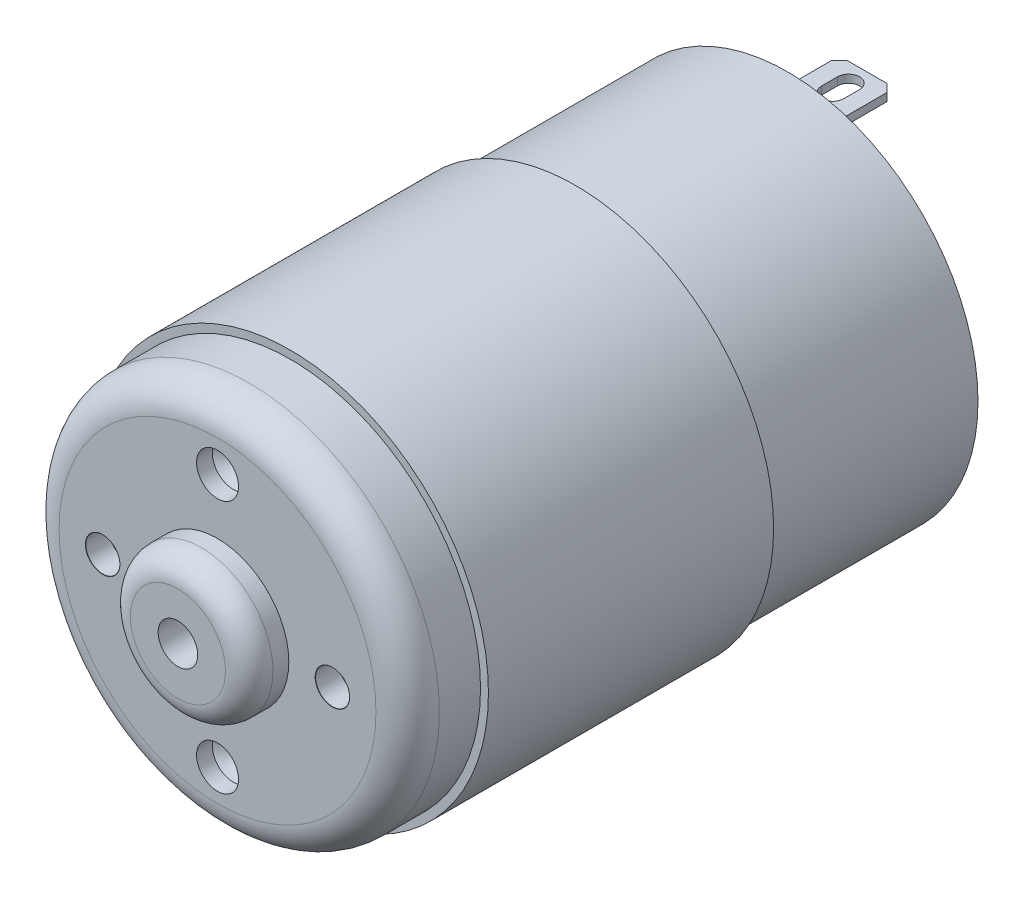
SolidWorks part; units mm, degrees
ref_plane "Front Plane" through (0, 0, 0) normal (1, 0, 0) x (0, 1, 0)
ref_plane "Top Plane" through (0, 0, 0) normal (0, 0, 1) x (0, 1, 0)
ref_plane "Right Plane" through (0, 0, 0) normal (0, 1, 0) x (-1, 0, 0)
sketch "Sketch1" plane through (0, 0, 0) normal (0, 0, 1) x (0, 1, 0)
  circle A0 centre (0, 0) radius 24
  dimension "D1" = 48
extrude "Boss-Extrude1" add sketch "Sketch1" along normal blind 72 contours A0
ref_plane "Plane1" through (0, 0, 72) normal (0, 0, 1) x (1, 0, 0)
sketch "Sketch6" plane through (0, 0, 72) normal (0, 0, 1) x (1, 0, 0)
  circle A0 centre (0, 0) radius 9
  dimension "D1" = 18
extrude "Boss-Extrude2" add sketch "Sketch6" along normal blind 5
sketch "Sketch7" plane through (0, 0, 0) normal (0, 0, 1) x (0, 1, 0)
  circle A0 centre (0, 0) radius 9
extrude "Boss-Extrude3" add sketch "Sketch7" against normal blind 5
ref_plane "Plane2" through (0, 0, 77) normal (0, 0, 1) x (1, 0, 0)
sketch "Sketch8" plane through (0, 0, 77) normal (0, 0, 1) x (1, 0, 0)
  circle A0 centre (0, 0) radius 2.5
  dimension "D1" = 5
extrude "Cut-Extrude5" cut sketch "Sketch8" against normal up to surface (82 mm away) up to face at (9, 0, -5)
fillet "Fillet3" radius 3 2 edges at (9, 0, -5) (9, 0, 77)
fillet "Fillet4" radius 4 1 edges at (24, 0, 72)
sketch "Sketch9" plane through (0, 0, 72) normal (0, 0, 1) x (1, 0, 0)
  circle A0 centre (0, 0) radius 24
  circle A1 centre (0, 0) radius 25
  dimension "D1" = 50
extrude "Boss-Extrude4" add sketch "Sketch9" against normal blind 36 from offset 9.2 offset against normal yes
sketch "Sketch10" plane through (0, 0, 0) normal (0, 0, 1) x (0, 1, 0)
  line L1 (-18, 3.5) -> (-19, 3.5)
  line L2 (-18, 3.5) -> (-18, -3.5)
  line L3 (-18, -3.5) -> (-19, -3.5)
  line L4 (-19, 3.5) -> (-19, -3.5)
  line L5 (18, -3.5) -> (19, -3.5)
  line L6 (19, 3.5) -> (19, -3.5)
  line L7 (18, 3.5) -> (19, 3.5)
  line L8 (18, 3.5) -> (18, -3.5)
  point P4 (-18, 0)
  dimension "D1" = 18
  dimension "D2" = 0
  dimension "D3" = 7
  dimension "D4" = 1
extrude "Boss-Extrude5" add sketch "Sketch10" against normal blind 10
sketch "Sketch15" plane through (0, 0, 72) normal (0, 0, 1) x (1, 0, 0)
  point P0 (0, 0)
  point P5 (-14.5, 0)
  point P7 (14.5, 0)
  dimension "D1" = 14.5
  dimension "D2" = 14.5
hole_wizard "M4 Clearance Hole5" positions "Sketch15" profile "Sketch18" hole size "M4" standard "ISO"
sketch "Sketch18" plane through (14.5, 0, 72) normal (1, 0, 0) x (0, -1, 0)
  line L0 (0, 0) -> (0, 4.2919)
  line L1 (0, 4.2919) -> (2.15, 3)
  line L2 (2.15, 3) -> (2.15, 0.025)
  line L3 (2.15, 0.025) -> (2.175, 0)
  line L5 (2.175, 0) -> (0, 0)
  line L6 (-2.15, 0.025) -> (-2.175, 0) construction
  line L10 (0, 4.2919) -> (-2.15, 3) construction
  line L11 (0, -6.35) -> (0, 107.95) construction
  dimension "Hole Dia." = 4.3
  dimension "Hole Depth" = 3
  dimension "Near C'Sink Dia." = 4.35
  dimension "Near C'Sink Angle" = 90
  dimension "Drill Angle" = 118
sketch "Sketch19" plane through (0, 0, 77) normal (0, 0, 1) x (1, 0, 0)
  point P0 (0, 16)
  point P5 (0, 0)
  point P7 (0, -16)
  dimension "D1" = 16
  dimension "D2" = 16
hole_wizard "M5 Clearance Hole1" positions "Sketch19" profile "Sketch20" hole size "M5" standard "ISO"
sketch "Sketch20" plane through (0, 16, 77) normal (1, 0, 0) x (0, -1, 0)
  line L0 (0, 0) -> (0, 8.5923)
  line L1 (0, 8.5923) -> (2.65, 7)
  line L2 (2.65, 7) -> (2.65, 0.025)
  line L3 (2.65, 0.025) -> (2.675, 0)
  line L5 (2.675, 0) -> (0, 0)
  line L6 (-2.65, 0.025) -> (-2.675, 0) construction
  line L10 (0, 8.5923) -> (-2.65, 7) construction
  line L11 (0, -6.35) -> (0, 107.95) construction
  dimension "Hole Dia." = 5.3
  dimension "Hole Depth" = 7
  dimension "Near C'Sink Dia." = 5.35
  dimension "Near C'Sink Angle" = 90
  dimension "Drill Angle" = 118
sketch "Sketch21" plane through (0, -19, 0) normal (0, -1, 0) x (1, 0, 0)
  line L0 (-3, -0.0166) -> (-3, -1.8436)
  line L1 (-3, -1.8436) -> (-3.5, -2.3)
  line L2 (-3.5, -2.3) -> (-3.5, -9)
  line L3 (-3.5, -9) -> (-2.5873, -10)
  line L4 (-2.5873, -10) -> (2.5, -10)
  line L5 (2.5, -10) -> (3.5, -9)
  line L6 (3.5, -9) -> (3.5, -2.3)
  line L7 (3.5, -2.3) -> (3, -1.8)
  line L8 (3, -1.8) -> (3, -0.0166)
  line L9 (3, -0.0166) -> (-3, -0.0166)
  line L10 (-3.5, -10) -> (-3.5, 0) construction
  line L12 (-3.5, -10) -> (3.5, -10) construction
  line L13 (-3.5, -2.3) -> (-3.5, 0)
  line L14 (-3.5, 0) -> (-3, -0.0166)
  line L15 (3, -0.0166) -> (3.5, 0)
  line L16 (3.5, 0) -> (3.5, -2.3)
  line L17 (3.5, -9) -> (3.5, -10)
  line L18 (3.5, -10) -> (2.5, -10)
  line L19 (-3.5, -9) -> (-3.5, -10)
  line L20 (-3.5, -10) -> (-2.5873, -10)
  line L21 (0, -7.5) -> (0, -5.5) construction
  line L22 (-1.3944, -7.5) -> (-1.3944, -5.5)
  line L23 (1.3944, -7.5) -> (1.3944, -5.5)
  arc A0 (-1.3944, -7.5) -> (1.3944, -7.5) centre (0, -7.5) ccw
  arc A1 (1.3944, -5.5) -> (-1.3944, -5.5) centre (0, -5.5) ccw
  point P25 (0, -6.5)
  dimension "D1" = 0.5
  dimension "D2" = 1
  dimension "D3" = 1
  dimension "D4" = 2
  dimension "D5" = 1.5
  dimension "D6" = 2.3
  dimension "D7" = 2.3
  dimension "D8" = 6
extrude "Cut-Extrude7" cut sketch "Sketch21" against normal up to surface (1 mm away)
sketch "Sketch23" plane through (0, 19, 0) normal (0, 1, 0) x (-1, 0, 0)
  line L0 (-3, -0.0166) -> (-3, -1.8436)
  line L1 (-3, -1.8436) -> (-3.5, -2.3436)
  line L2 (-3.5, -2.3436) -> (-3.5, -9)
  line L3 (-3.5, -9) -> (-2.5, -10)
  line L4 (-2.5, -10) -> (2.5, -10)
  line L5 (2.5, -10) -> (3.5, -9)
  line L6 (3.5, -9) -> (3.5, -2.3904)
  line L7 (3.5, -2.3904) -> (3.0251, -1.9155)
  line L8 (3.0251, -1.9155) -> (3.0251, -0.0166)
  line L9 (3.0251, -0.0166) -> (-3, -0.0166)
  line L10 (-3.5, -2.3436) -> (-3.5, 0)
  line L11 (-3.5, 0) -> (-3, -0.0166)
  line L12 (3.0251, -0.0166) -> (3.5, 0)
  line L13 (3.5, 0) -> (3.5, -2.3904)
  line L14 (3.5, -9) -> (3.5, -10)
  line L15 (3.5, -10) -> (2.5, -10)
  line L16 (-3.5, -9) -> (-3.5, -10)
  line L17 (-3.5, -10) -> (-2.5, -10)
  line L18 (-0.0524, -7.6056) -> (-0.0524, -5.6056) construction
  line L19 (-1.4468, -7.6056) -> (-1.4468, -5.6056)
  line L20 (1.3421, -7.6056) -> (1.3421, -5.6056)
  arc A0 (-1.4468, -7.6056) -> (1.3421, -7.6056) centre (-0.0524, -7.6056) ccw
  arc A1 (1.3421, -5.6056) -> (-1.4468, -5.6056) centre (-0.0524, -5.6056) ccw
  point P16 (-0.0524, -6.6056)
  point P21 (-0.0524, -5.4713)
  point P22 (-0.0524, -5.4713)
  point P24 (-0.0103, -7.8401)
  point P29 (-0.0524, -9)
  dimension "D1" = 2
extrude "Cut-Extrude8" cut sketch "Sketch23" against normal up to surface (1 mm away)
